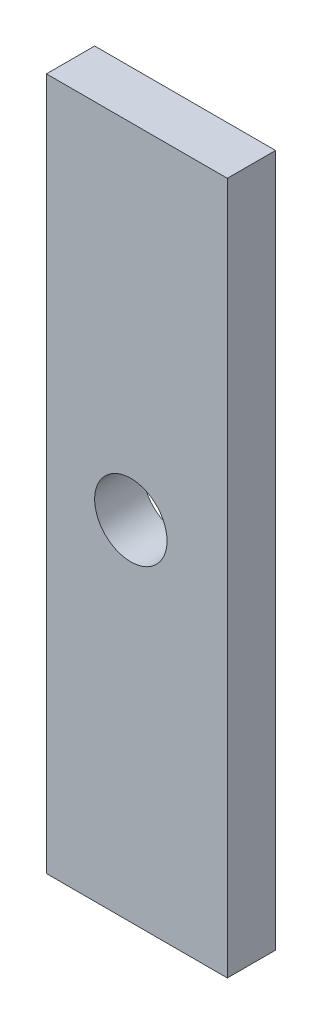
SolidWorks part; units mm, degrees
ref_plane "Front Plane" through (0, 0, 0) normal (0, 0, 1) x (1, 0, 0)
ref_plane "Top Plane" through (0, 0, 0) normal (0, 1, 0) x (1, 0, 0)
ref_plane "Right Plane" through (0, 0, 0) normal (1, 0, 0) x (0, 0, -1)
sketch "Sketch1" plane through (0, 0, 0) normal (0, 0, 1) x (1, 0, 0)
  line L0 (-3.5, 14.272) -> (4, 14.272)
  line L1 (-3.5, -14.441) -> (4, -14.441)
  line L2 (4, -14.441) -> (4, 14.272)
  line L3 (-3.5, 14.272) -> (-3.5, -14.441)
  circle A0 centre (0, 0) radius 1.5
  dimension "D1" = 3
  dimension "D4" = 14.272
  dimension "D2" = 4
  dimension "D3" = 3.5
  dimension "D5" = 14.441
extrude "Boss-Extrude1" add sketch "Sketch1" along normal blind 2
equation "\"D5@Sketch1\"= \"D76@Sketch1@palmUp.SLDPRT\" - 6.72 - 0.41'Support Pully Thumb Palm Up"
